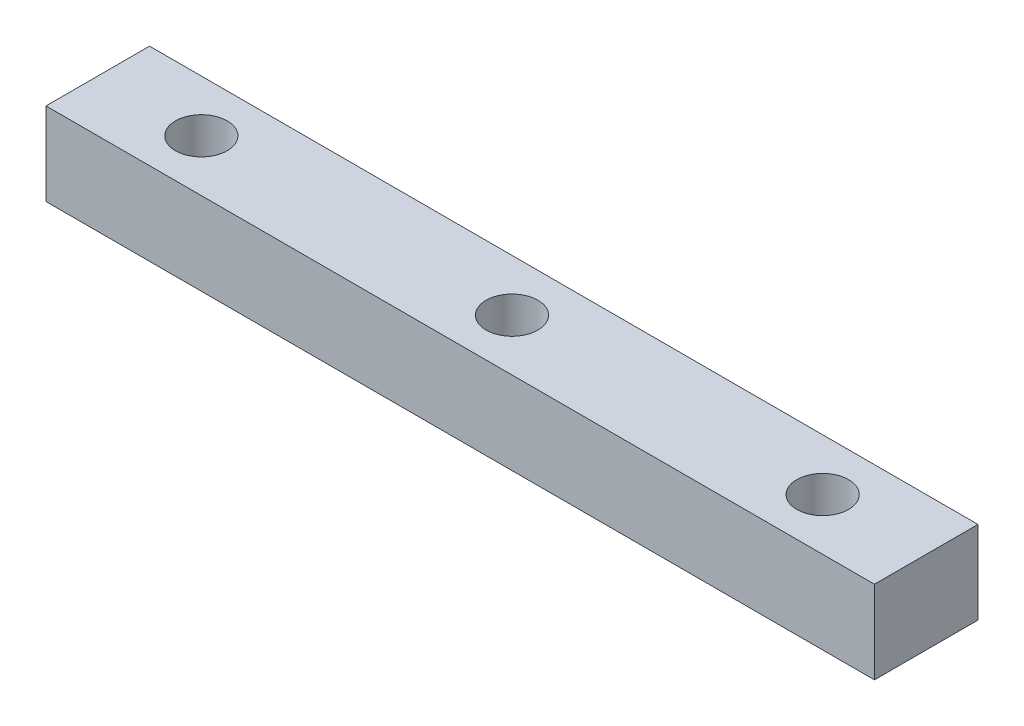
SolidWorks part; units mm, degrees
ref_plane "정면" through (0, 0, 0) normal (0, 0, 1) x (1, 0, 0)
ref_plane "윗면" through (0, 0, 0) normal (0, 1, 0) x (1, 0, 0)
ref_plane "우측면" through (0, 0, 0) normal (1, 0, 0) x (0, 0, -1)
sketch "스케치1" plane through (0, 0, 0) normal (0, 1, 0) x (1, 0, 0)
  line L1 (20, 2.5) -> (-20, 2.5)
  line L2 (20, 2.5) -> (20, -2.5)
  line L3 (20, -2.5) -> (-20, -2.5)
  line L4 (-20, 2.5) -> (-20, -2.5)
  circle A0 centre (0, 0) radius 1.25
  circle A1 centre (15, 0) radius 1.25
  circle A2 centre (-15, 0) radius 1.25
  point P4 (0, 2.5)
  point P6 (20, 0)
  dimension "D3" = 2.5
  dimension "D1" = 15
  dimension "D2" = 15
  dimension "D4" = 40
  dimension "D5" = 5
extrude "보스-돌출1" add sketch "스케치1" along normal blind 4
